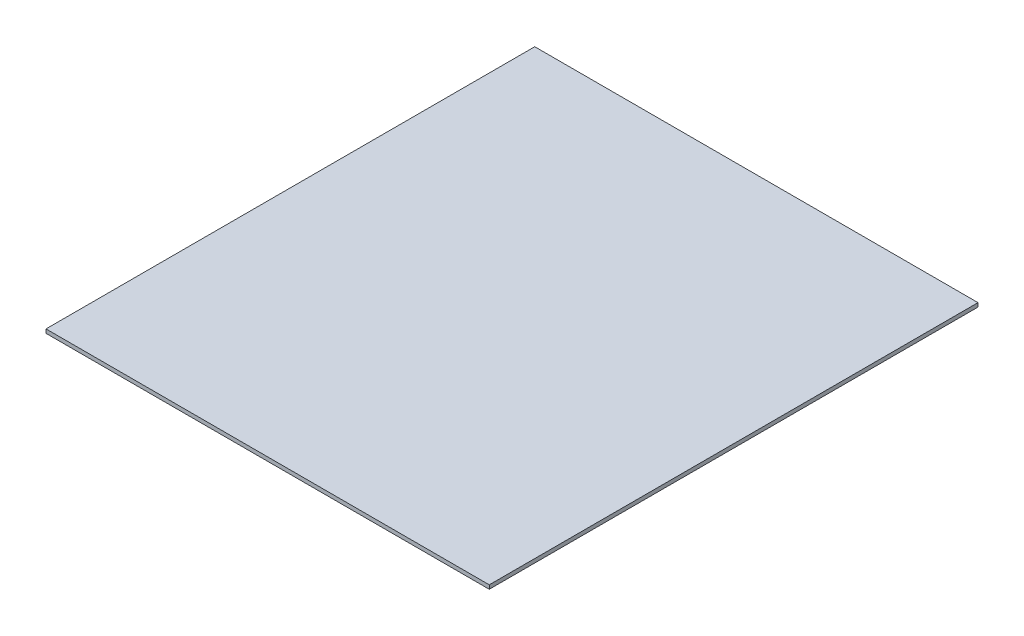
SolidWorks part; units mm, degrees
material "6061-T6 (SS)"
ref_plane "Front Plane" through (0, 0, 0) normal (0, 0, 1) x (1, 0, 0)
ref_plane "Top Plane" through (0, 0, 0) normal (0, 1, 0) x (1, 0, 0)
ref_plane "Right Plane" through (0, 0, 0) normal (1, 0, 0) x (0, 0, -1)
sketch "Sketch1" plane through (0, 0, 0) normal (0, 1, 0) x (1, 0, 0)
  line L1 (0, 0) -> (458, 0)
  line L2 (0, 0) -> (0, 505)
  line L3 (0, 505) -> (458, 505)
  line L4 (458, 0) -> (458, 505)
  dimension "D1" = 505
  dimension "D2" = 458
extrude "Boss-Extrude1" add sketch "Sketch1" along normal blind 4
